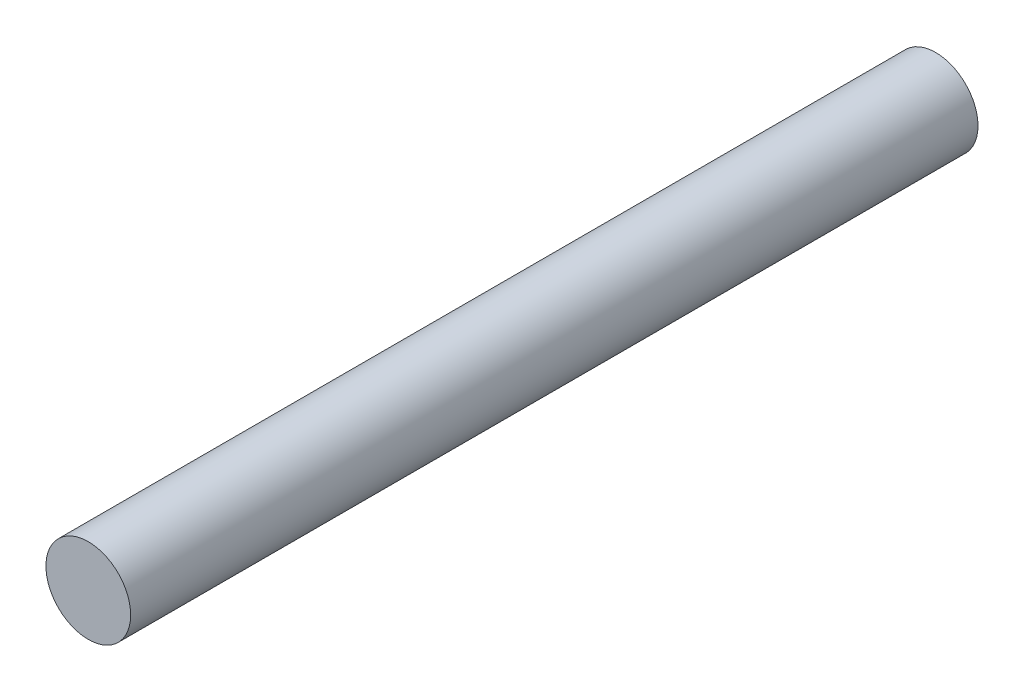
SolidWorks part; units mm, degrees
ref_plane "Front Plane" through (0, 0, 0) normal (0, 0, 1) x (1, 0, 0)
ref_plane "Top Plane" through (0, 0, 0) normal (0, 1, 0) x (1, 0, 0)
ref_plane "Right Plane" through (0, 0, 0) normal (1, 0, 0) x (0, 0, -1)
sketch "Sketch1" plane through (0, 0, 0) normal (0, 0, 1) x (1, 0, 0)
  circle A0 centre (0, 0) radius 3.175
  dimension "D1" = 6.35
extrude "Boss-Extrude1" add sketch "Sketch1" along normal blind 63.5
